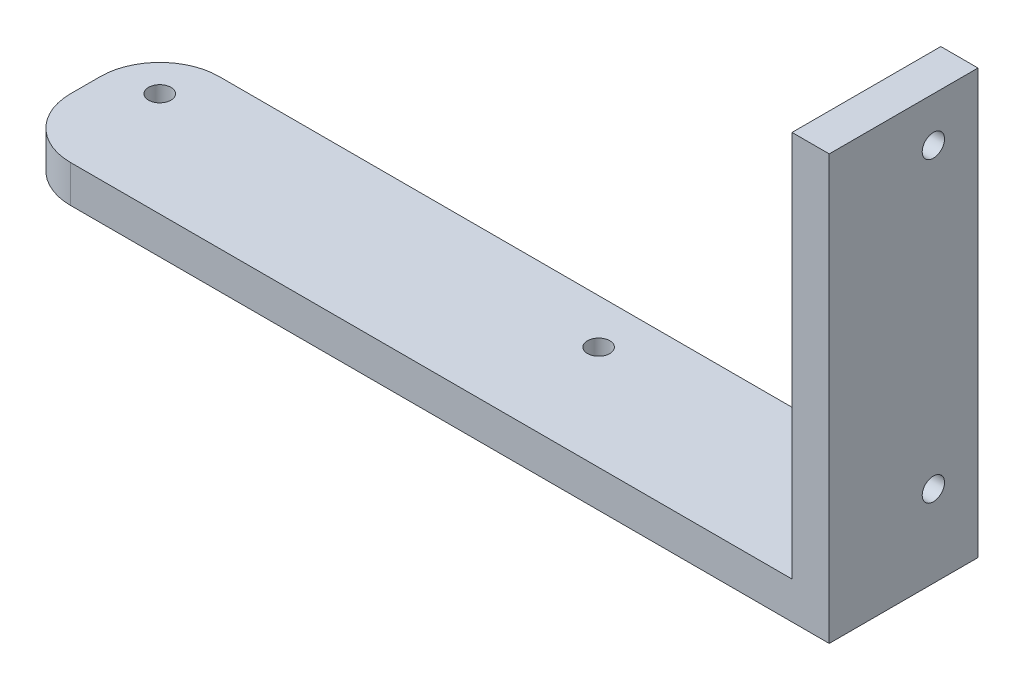
SolidWorks part; units mm, degrees
ref_plane "Front Plane" through (0, 0, 0) normal (0, 0, 1) x (1, 0, 0)
ref_plane "Top Plane" through (0, 0, 0) normal (0, 1, 0) x (1, 0, 0)
ref_plane "Right Plane" through (0, 0, 0) normal (1, 0, 0) x (0, 0, -1)
sketch "Sketch1" plane through (0, 0, 0) normal (0, 1, 0) x (1, 0, 0)
  line L1 (0, 0) -> (110, 0)
  line L2 (0, 0) -> (0, 20)
  line L3 (0, 20) -> (110, 20)
  line L4 (110, 0) -> (110, 20)
  dimension "D1" = 110
  dimension "D2" = 20
extrude "Boss-Extrude1" add sketch "Sketch1" along normal blind 5
sketch "Sketch2" plane through (0, 5, 0) normal (0, 1, 0) x (1, 0, 0)
  line L0 (110, 20) -> (0, 20) construction
  line L1 (110, 0) -> (105, 0)
  line L2 (110, 0) -> (110, 20)
  line L3 (110, 20) -> (105, 20)
  line L4 (105, 0) -> (105, 20)
  dimension "D1" = 5
extrude "Boss-Extrude2" add sketch "Sketch2" along normal blind 52
sketch "Sketch3" plane through (0, 5, 0) normal (0, 1, 0) x (1, 0, 0)
  line L0 (0, 20) -> (0, 0) construction
  line L2 (105, 20) -> (0, 20) construction
  circle A0 centre (6, 14) radius 1.5
  circle A1 centre (65, 14) radius 1.5
  dimension "D1" = 3
  dimension "D2" = 6
  dimension "D3" = 6
  dimension "D4" = 59
extrude "Cut-Extrude1" cut sketch "Sketch3" against normal through all
fillet "Fillet1" radius 8 2 edges at (0, 2.5, 0) (0, 2.5, -20)
sketch "Sketch4" plane through (105, 0, 0) normal (-1, 0, 0) x (0, 0, 1)
  line L1 (-20, 5) -> (0, 5) construction
  line L4 (-20, 57) -> (-20, 5) construction
  circle A0 centre (-14, 11) radius 1.5
  circle A2 centre (-14, 51) radius 1.5
  dimension "D1" = 6
  dimension "D2" = 3
  dimension "D3" = 6
  dimension "D4" = 40
extrude "Cut-Extrude2" cut sketch "Sketch4" against normal through all
